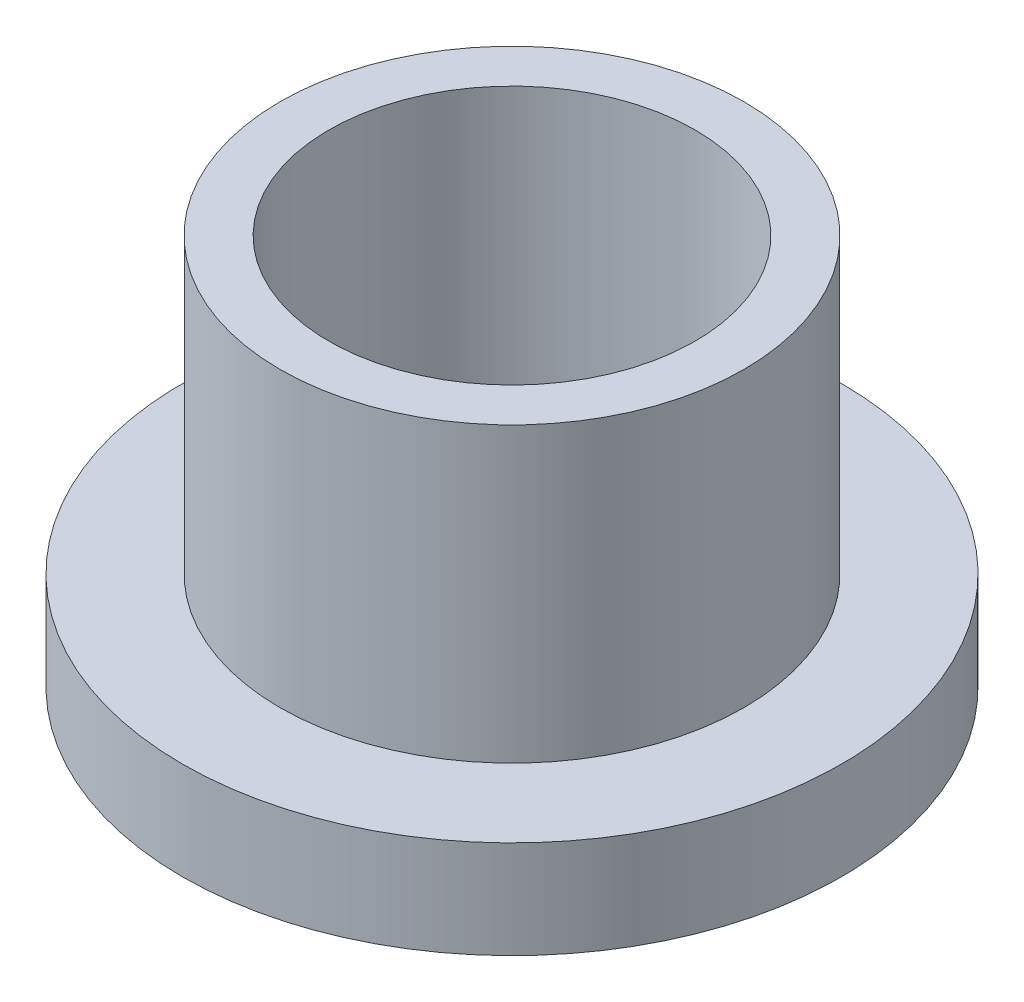
SolidWorks part; units mm, degrees
ref_plane "Front Plane" through (0, 0, 0) normal (0, 0, 1) x (1, 0, 0)
ref_plane "Top Plane" through (0, 0, 0) normal (0, 1, 0) x (1, 0, 0)
ref_plane "Right Plane" through (0, 0, 0) normal (1, 0, 0) x (0, 0, -1)
sketch "Sketch1" plane through (0, 0, 0) normal (0, 0, 1) x (1, 0, 0)
  line L0 (1.5, 0) -> (2.7, 0)
  line L1 (2.7, 0) -> (2.7, 0.8)
  line L2 (2.7, 0.8) -> (1.9, 0.8)
  line L3 (1.9, 0.8) -> (1.9, 3.2)
  line L4 (1.9, 3.2) -> (1.5, 3.2)
  line L5 (1.5, 3.2) -> (1.5, 0)
  line L6 (0, 0) -> (0, 3.2) construction
  point P9 (0, 0)
  dimension "D1" = 2.4
  dimension "D2" = 0.8
  dimension "D3" = 3
  dimension "D4" = 3.8
  dimension "D5" = 0.8
revolve "Revolve1" add sketch "Sketch1" angle 360 about L6
chamfer "Chamfer1" distance 0.2 angle 45 1 edges at (0, 0, -1.5)
